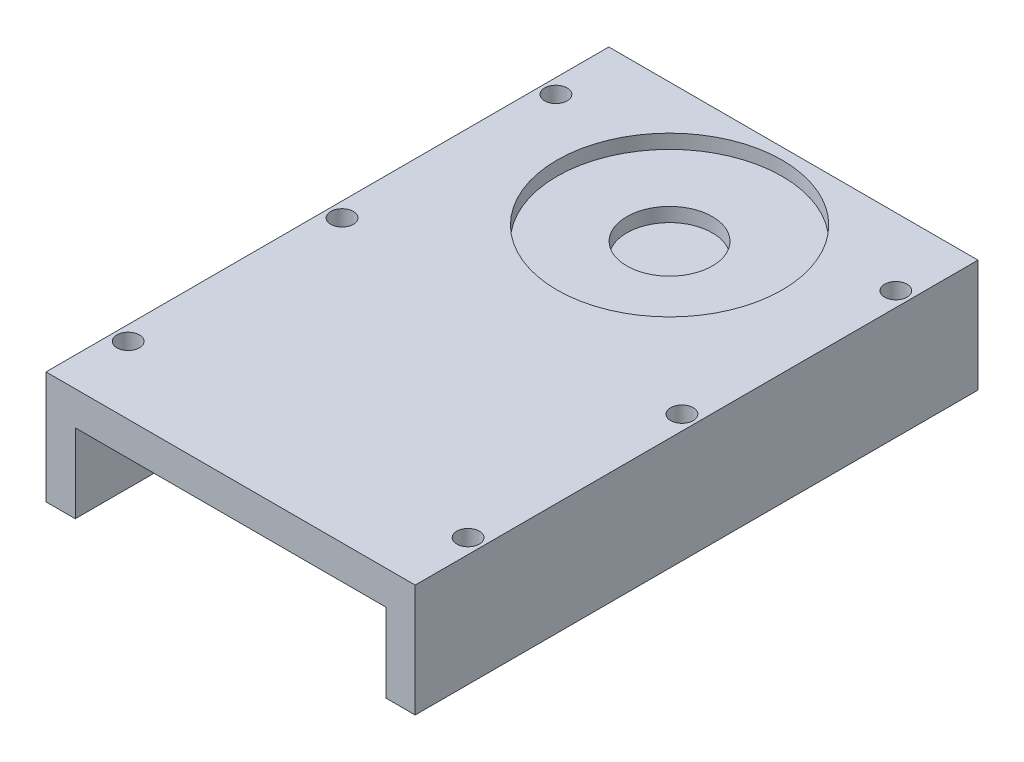
SolidWorks part; units mm, degrees
ref_plane "Front Plane" through (0, 0, 0) normal (0, 0, 1) x (1, 0, 0)
ref_plane "Top Plane" through (0, 0, 0) normal (0, 1, 0) x (1, 0, 0)
ref_plane "Right Plane" through (0, 0, 0) normal (1, 0, 0) x (0, 0, -1)
sketch "Sketch2" plane through (0, 0, 0) normal (0, 0, 1) x (1, 0, 0)
  line L0 (-18.3145, 3.81) -> (20.828, 3.81)
  line L1 (20.828, 3.81) -> (20.828, -8.89)
  line L2 (20.828, -8.89) -> (17.526, -8.89)
  line L3 (17.526, -8.89) -> (17.526, 0)
  line L4 (17.526, 0) -> (-17.526, 0)
  line L5 (-17.526, 0) -> (-17.526, -8.89)
  line L6 (-17.526, -8.89) -> (-20.828, -8.89)
  line L7 (-20.828, -8.89) -> (-20.828, 3.81)
  line L8 (-20.828, 3.81) -> (-18.3145, 3.81)
  point P3 (-20.828, 8.3413)
  point P16 (0, -2.4068)
  dimension "D1" = 8.89
  dimension "D2" = 3.302
  dimension "D3" = 35.052
  dimension "D4" = 12.7
extrude "Boss-Extrude1" add sketch "Sketch2" along normal blind 63.5
sketch "Sketch3" plane through (-20.828, 0, 0) normal (-1, 0, 0) x (0, 0, 1)
  line L0 (63.5, -8.89) -> (63.5, -2.54) construction
  line L1 (63.5, -8.89) -> (0, -8.89) construction
  line L2 (63.5, -2.54) -> (0, -2.54) construction
  line L3 (0, 3.81) -> (0, -8.89) construction
  line L4 (63.5, 3.81) -> (63.5, -8.89) construction
  line L5 (32.685, -2.54) -> (32.685, -8.89) construction
  line L6 (7.62, -5.715) -> (33.655, -5.715) construction
  line L7 (33.655, -5.715) -> (59.69, -5.715) construction
  circle A0 centre (59.69, -5.715) radius 1.27
  circle A1 centre (7.62, -5.715) radius 1.27
  circle A2 centre (33.655, -5.715) radius 1.27
  point P14 (32.685, -5.715)
  dimension "D2" = 2.54
  dimension "D1" = 6.35
  dimension "D3" = 7.62
  dimension "D4" = 7.62
sketch "Sketch4" plane through (0, -8.89, 0) normal (0, -1, 0) x (1, 0, 0)
  line L0 (-20.828, 7.2541) -> (-17.526, 7.2541) construction
  line L1 (-20.828, 63.5) -> (-20.828, 0) construction
  line L2 (-17.526, 63.5) -> (-17.526, 0) construction
  line L3 (-20.828, 0) -> (-17.526, 0) construction
  line L4 (-20.828, 63.5) -> (-17.526, 63.5) construction
  line L5 (-19.177, 55.88) -> (-19.177, 31.75) construction
  line L6 (-19.177, 31.75) -> (-19.177, 7.62) construction
  circle A0 centre (-19.177, 7.62) radius 1.27
  circle A1 centre (-19.177, 55.88) radius 1.27
  circle A2 centre (-19.177, 31.75) radius 1.27
  point P8 (-19.177, 7.2541)
  dimension "D1" = 2.54
  dimension "D2" = 7.62
  dimension "D3" = 7.62
extrude "Cut-Extrude2" cut sketch "Sketch4" against normal blind 63.5
mirror "Mirror1" about plane through (0, 0, 0) normal (1, 0, 0) of "Cut-Extrude2"
sketch "Sketch6" plane through (0, 3.81, 0) normal (0, 1, 0) x (1, 0, 0)
  line L0 (-20.828, -16.6324) -> (20.828, -16.6324) construction
  line L1 (-20.828, -7.62) -> (-20.828, -33.655) construction
  line L2 (20.828, -63.5) -> (20.828, 0) construction
  circle A0 centre (0, -13.97) radius 12.7
  point P9 (0, -16.6324)
  dimension "D1" = 25.4
  dimension "D2" = 13.97
extrude "Cut-Extrude7" cut sketch "Sketch6" against normal blind 1.5875
sketch "Sketch8" plane through (0, 2.2225, 0) normal (0, 1, 0) x (1, 0, 0)
  circle A0 centre (0, -13.97) radius 4.826
  dimension "D1" = 9.652
extrude "Cut-Extrude8" cut sketch "Sketch8" against normal blind 1.5875
